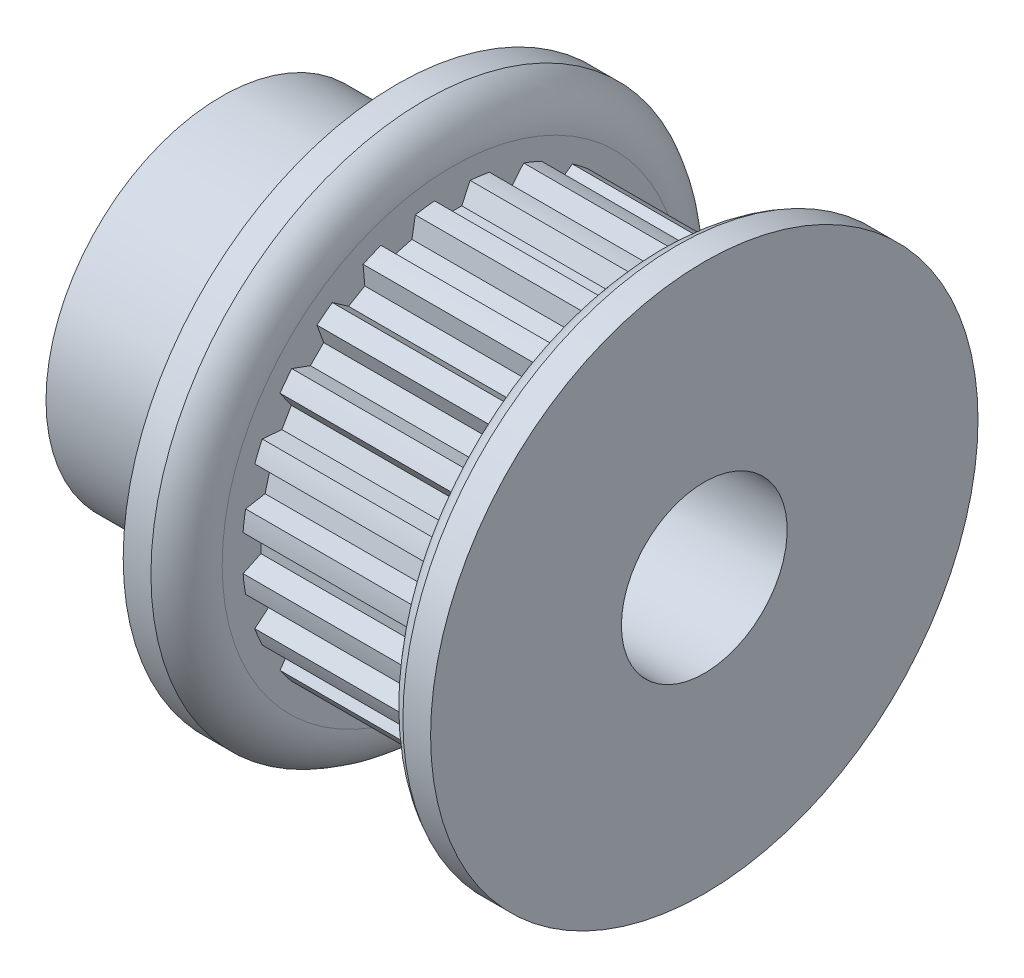
SolidWorks part; units mm, degrees
ref_plane "Front Plane" through (0, 0, 0) normal (0, 0, 1) x (1, 0, 0)
ref_plane "Top Plane" through (0, 0, 0) normal (0, 1, 0) x (1, 0, 0)
ref_plane "Right Plane" through (0, 0, 0) normal (1, 0, 0) x (0, 0, -1)
sketch "Sketch2" plane through (0, 0, 0) normal (1, 0, 0) x (0, 0, -1)
  line L3 (0, 0) -> (0, 6.9342) construction
  line L6 (0, -7.4422) -> (0, -7.7597) construction
  line L7 (-0.5715, 7.4202) -> (-0.341, 6.9258)
  line L8 (0.5715, 7.4202) -> (0.341, 6.9258)
  line L9 (-0.5715, 7.4202) -> (-0.6431, 7.5737)
  line L10 (0.5715, 7.4202) -> (0.6431, 7.5737)
  line L12 (-0.341, 6.9258) -> (0.341, 6.9258)
  line L14 (0, 7.4422) -> (0, 7.7597) construction
  line L15 (0, 0) -> (0, -1.143) construction
  circle A0 centre (0, 0) radius 7.7597 construction
  circle A1 centre (0, 0) radius 6.9342 construction
  circle A2 centre (0, 0) radius 7.4422 construction
  arc A7 (0.6431, 7.5737) -> (-0.6431, 7.5737) centre (0, 0) ccw
  point P5 (0, 7.6009)
  dimension "D3" = 0.3175
  dimension "D1" = 50
sketch "Sketch1" plane through (0, 0, 0) normal (0, 0, 1) x (1, 0, 0)
  line L0 (-8.7376, 0) -> (8.7376, 0) construction
  line L1 (-8.7376, 2.3813) -> (8.7376, 2.3813)
  line L2 (-8.7376, 2.3813) -> (-8.7376, 6.35)
  line L3 (-2.3876, 9.906) -> (-1.3843, 9.906)
  line L4 (-0.381, 7.7597) -> (-0.381, 8.3312)
  line L5 (-0.381, 8.9027) -> (-0.381, 7.7597) construction
  line L6 (-0.381, 7.7597) -> (6.731, 7.7597)
  line L7 (6.731, 7.7597) -> (6.731, 8.3312)
  line L8 (6.731, 7.7597) -> (8.7376, 7.7597) construction
  line L9 (7.7343, 9.906) -> (8.7376, 9.906)
  line L10 (8.7376, 9.906) -> (8.7376, 2.3813)
  line L11 (7.7343, 7.7597) -> (7.7343, 9.906) construction
  line L12 (-5.5626, 6.35) -> (-5.5626, 2.3812) construction
  line L13 (-2.3876, 9.906) -> (-2.3876, 6.35)
  line L14 (-2.3876, 6.35) -> (-8.7376, 6.35)
  arc A0 (6.731, 8.3312) -> (7.7343, 9.906) centre (8.4686, 8.3312) cw
  arc A1 (-0.381, 8.3312) -> (-1.3843, 9.906) centre (-2.1186, 8.3312) ccw
  dimension "Bore Size" = 4.7625
  dimension "Overall Width" = 17.4752
  dimension "Inside Width" = 7.112
  dimension "OD" = 19.812
  dimension "D2" = 15.5194
  dimension "D3" = 1.143
  dimension "D4" = 0.5715
  dimension "Outside Width" = 11.1252
revolve "Revolve1" add sketch "Sketch1" angle 360 mid plane about L0
sketch "Sketch4" plane through (-0.381, 0, 0) normal (1, 0, 0) x (0, 0, -1)
  circle A0 centre (0, 0) radius 7.601
  circle A2 centre (0, 0) radius 7.7597
  circle A3 centre (0, 0) radius 7.7597 construction
extrude "Cut-Extrude2" cut sketch "Sketch4" along normal up to surface (7.112 mm away) up to face at (6.731, 0, 7.7597)
sketch "Sketch3" plane through (-0.381, 0, 0) normal (1, 0, 0) x (0, 0, -1)
  line L2 (-0.5715, 7.4202) -> (-0.341, 6.9258) construction
  line L3 (-0.341, 6.9258) -> (0.341, 6.9258) construction
  line L4 (0.5715, 7.4202) -> (0.341, 6.9258) construction
  line L5 (-0.6431, 7.5737) -> (-0.341, 6.9258)
  line L6 (-0.341, 6.9258) -> (0.341, 6.9258)
  line L7 (0.6431, 7.5737) -> (0.341, 6.9258)
  arc A1 (0.6431, 7.5737) -> (-0.6431, 7.5737) centre (0, 0) ccw construction
  arc A2 (0.6431, 7.5737) -> (-0.6431, 7.5737) centre (0, 0) ccw
extrude "Cut-Extrude1" cut sketch "Sketch3" along normal up to surface (7.112 mm away) up to face at (6.731, 0, 8.3312)
pattern_circular "CirPattern1" count 24 over 360 about axis through (0, 0, 0) along (1, 0, 0) of "Cut-Extrude1"
sketch "Sketch5" plane through (0, 0, 0) normal (0, 0, 1) x (1, 0, 0)
  line L1 (6.731, 8.3312) -> (6.731, -8.3312) construction
  point P0 (6.731, 0)
sketch "Sketch6" plane through (-8.7376, 0, 0) normal (-1, 0, 0) x (0, 0, 1)
  circle A0 centre (0, 0) radius 3
  dimension "D1" = 6
extrude "Cut-Extrude3" cut sketch "Sketch6" against normal through all
equation "\"D3@Sketch2\" = (\"hs@Sketch2\"-\"ht@Sketch2\")/2"
equation "\"D2@Sketch1\" = \"PD@Sketch2\""
equation "\"D3@Sketch1\" = \"hs@Sketch2\""
equation "\"D4@Sketch1\" = \"D3@Sketch1\"/2"
